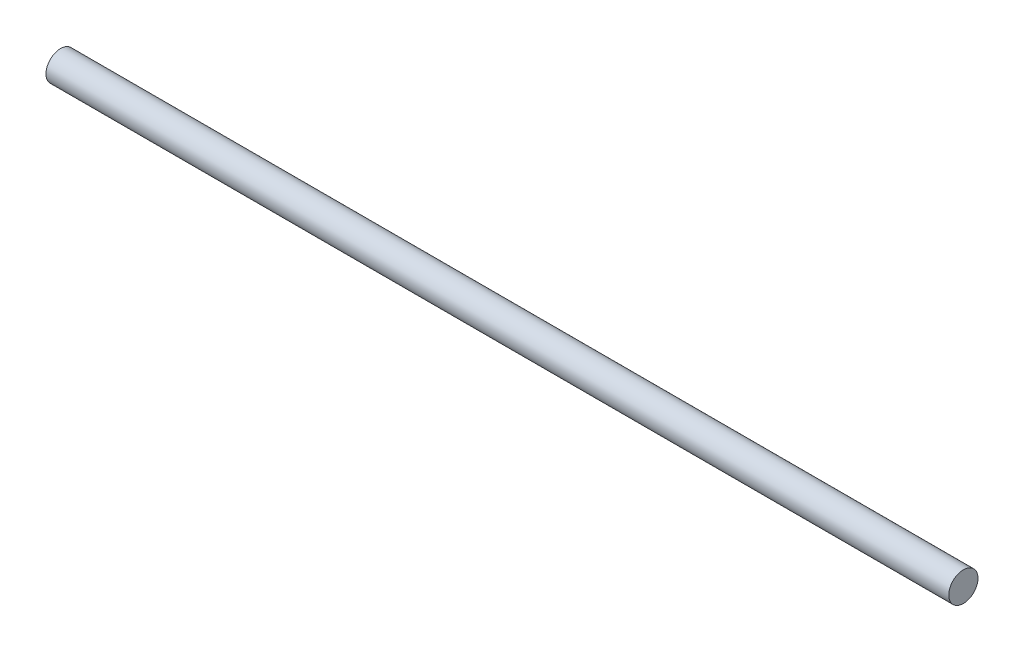
SolidWorks part; units mm, degrees
material "AISI 304"
ref_plane "Přední rovina" through (0, 0, 0) normal (0, 0, 1) x (1, 0, 0)
ref_plane "Horní rovina" through (0, 0, 0) normal (0, 1, 0) x (1, 0, 0)
ref_plane "Pravá rovina" through (0, 0, 0) normal (1, 0, 0) x (0, 0, -1)
sketch "Skica1" plane through (0, 0, 0) normal (1, 0, 0) x (0, 0, -1)
  circle A0 centre (0, 0) radius 1.15
  dimension "D1" = 2.3
extrude "Přidat vysunutím1" add sketch "Skica1" along normal blind 71
